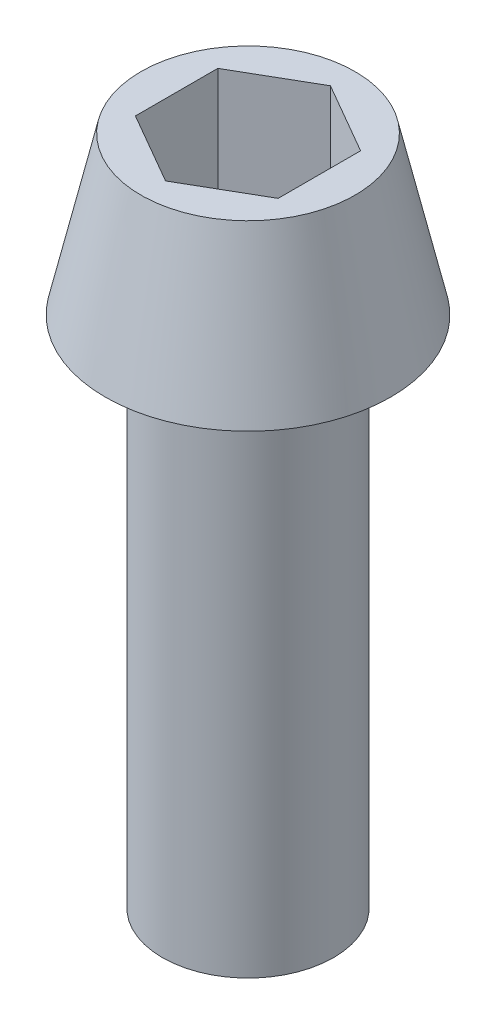
SolidWorks part; units mm, degrees
ref_plane "Plan de face" through (0, 0, 0) normal (0, 0, 1) x (1, 0, 0)
ref_plane "Plan de dessus" through (0, 0, 0) normal (0, 1, 0) x (1, 0, 0)
ref_plane "Plan de droite" through (0, 0, 0) normal (1, 0, 0) x (0, 0, -1)
sketch "Esquisse1" plane through (0, 0, 0) normal (0, 0, 1) x (1, 0, 0)
  line L0 (0, -18) -> (0, 5.5)
  line L1 (0, 5.5) -> (-3.75, 5.5)
  line L2 (-3.75, 5.5) -> (-5, 0)
  line L3 (-5, 0) -> (-3, 0)
  line L4 (-3, 0) -> (-3, -18)
  line L5 (-3, -18) -> (0, -18)
  line L6 (0, 21.1331) -> (0, -22.8738) construction
  dimension "D1" = 5.5
  dimension "D2" = 6
  dimension "D3" = 10
  dimension "D4" = 7.5
  dimension "D5" = 18
revolve "Révolution1" add sketch "Esquisse1" angle 360 about L6
sketch "Esquisse2" plane through (0, 5.5, 0) normal (0, 1, 0) x (-1, 0, 0)
  line L1 (0, -2.8868) -> (2.5, -1.4434)
  line L2 (2.5, -1.4434) -> (2.5, 1.4434)
  line L3 (2.5, 1.4434) -> (0, 2.8868)
  line L4 (0, 2.8868) -> (-2.5, 1.4434)
  line L5 (-2.5, 1.4434) -> (-2.5, -1.4434)
  line L6 (-2.5, -1.4434) -> (0, -2.8868)
  circle A0 centre (0, 0) radius 2.5 construction
  dimension "D1" = 5
extrude "Enlèv. mat.-Extru.1" cut sketch "Esquisse2" against normal blind 4
